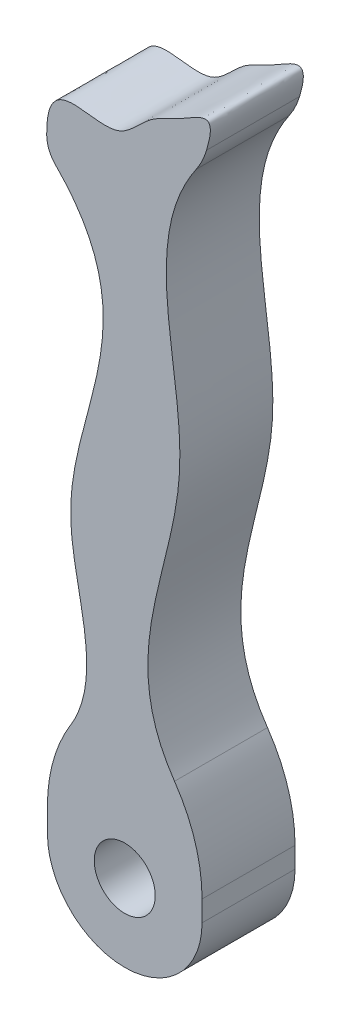
SolidWorks part; units mm, degrees
ref_plane "Front Plane" through (0, 0, 0) normal (0, 0, 1) x (1, 0, 0)
ref_plane "Top Plane" through (0, 0, 0) normal (0, 1, 0) x (1, 0, 0)
ref_plane "Right Plane" through (0, 0, 0) normal (1, 0, 0) x (0, 0, -1)
sketch "Sketch1" plane through (0, 0, 0) normal (0, 0, 1) x (1, 0, 0)
  line L0 (4.99, 0) -> (4.99, -9.98) construction
  line L2 (0, 0) -> (0, -9.98)
  line L3 (0, -9.98) -> (9.98, -9.98)
  line L4 (9.98, 0) -> (9.98, -9.98)
  circle A0 centre (4.99, -4.99) radius 1.9686
  spline S0 degree 3 poles (0, 33.1417) (-0.4755, 38.478) (3.9578, 34.8279) (6.4221, 38.3861) (9.1081, 39.295) (11.3297, 41.2413) (9.98, 37.4598) knots 0 0 0 0 0.419249 0.591046 0.727791 1 1 1 1
  spline S1 degree 3 poles (0, 33.1417) (7.1836, 26.5761) (-2.6792, 15.5093) (4.5622, 4.3347) (0, 0) knots 0 0 0 0 0.589573 1 1 1 1
  spline S2 degree 3 poles (9.98, 37.4598) (5.5822, 31.7548) (12.4925, 18.6724) (3.3408, 6.2217) (9.98, 0) knots 0 0 0 0 0.478051 1 1 1 1
  dimension "D3" = 3.9372
  dimension "D1" = 9.98
  dimension "D2" = 9.98
extrude "Boss-Extrude2" add sketch "Sketch1" along normal blind 6
fillet "Fillet4" radius 5 1 edges at (9.98, 37.4598, 3)
fillet "Fillet6" radius 2 1 edges at (0, 33.1417, 3)
fillet "Fillet7" radius 10 1 edges at (0, 0, 3)
fillet "Fillet8" radius 10 1 edges at (9.98, 0, 3)
fillet "Fillet10" radius 1 1 edges at (9.98, -9.98, 3)
fillet "Fillet11" radius 1 1 edges at (0, -9.98, 3)
sketch "Sketch2" plane through (0, 0, 6) normal (0, 0, 1) x (1, 0, 0)
  line L1 (0, -4.99) -> (11.8317, -4.99)
  line L2 (0, -4.99) -> (0, -12.1276)
  line L3 (0, -12.1276) -> (11.8317, -12.1276)
  line L4 (11.8317, -4.99) -> (11.8317, -12.1276)
  circle A0 centre (4.99, -4.99) radius 4.99
  line M1 (0, -3.4365) -> (0, -8.98)
  arc M2 (0, -8.98) -> (1, -9.98) centre (1, -8.98) ccw
  line M3 (1, -9.98) -> (8.98, -9.98)
  arc M4 (8.98, -9.98) -> (9.98, -8.98) centre (8.98, -8.98) ccw
  line M5 (9.98, -8.98) -> (9.98, -3.6572)
extrude "Cut-Extrude1" cut sketch "Sketch2" against normal blind 10 contours A0 M3 M4 M5 | A0 M1 M2 M3
